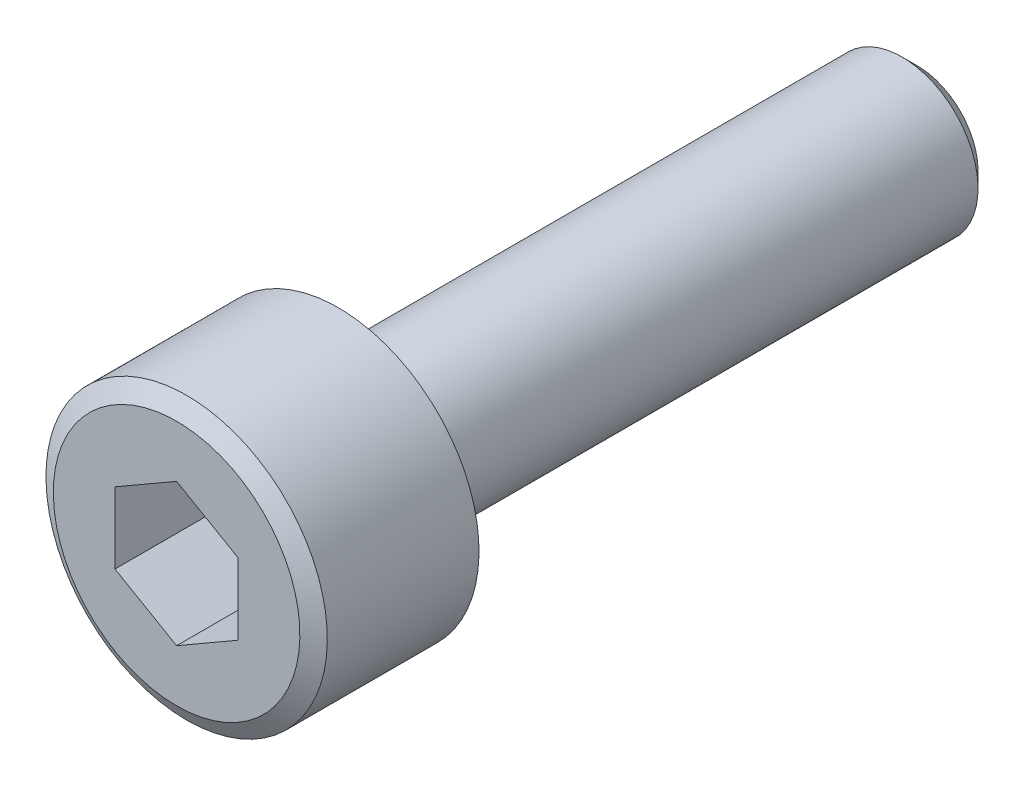
SolidWorks part; units mm, degrees
ref_plane "Front Plane" through (0, 0, 0) normal (0, 0, 1) x (1, 0, 0)
ref_plane "Top Plane" through (0, 0, 0) normal (0, 1, 0) x (1, 0, 0)
ref_plane "Right Plane" through (0, 0, 0) normal (1, 0, 0) x (0, 0, -1)
sketch "Sketch1" plane through (0, 0, 0) normal (1, 0, 0) x (0, 0, -1)
  line L0 (0, 0) -> (39.06, 0) construction
  line L1 (0, 0) -> (0, 6.5)
  line L2 (0, 6.5) -> (0.53, 7.418)
  line L3 (0.53, 7.418) -> (8.53, 7.418)
  line L4 (8.53, 7.418) -> (9.06, 6.5)
  line L5 (9.06, 6.5) -> (9.06, 4)
  line L6 (9.06, 4) -> (39.06, 4)
  line L7 (39.06, 4) -> (39.06, 0)
  line L8 (0, 0) -> (39.06, 0)
  dimension "D1" = 4
  dimension "D2" = 30
  dimension "D3" = 8
  dimension "D4" = 30
  dimension "D5" = 30
  dimension "D6" = 6.5
  dimension "D7" = 0.53
  dimension "D8" = 0.53
revolve "Revolve1" add sketch "Sketch1" angle 360 about L0
chamfer "Chamfer1" distance 0.8 angle 45 1 edges at (0, -4, -39.06)
sketch "Sketch2" plane through (0, 0, 0) normal (0, 0, 1) x (1, 0, 0)
  line L1 (-3.25, 1.8764) -> (-3.25, -1.8764)
  line L2 (-3.25, -1.8764) -> (0, -3.7528)
  line L3 (0, -3.7528) -> (3.25, -1.8764)
  line L4 (3.25, -1.8764) -> (3.25, 1.8764)
  line L5 (3.25, 1.8764) -> (0, 3.7528)
  line L6 (0, 3.7528) -> (-3.25, 1.8764)
  circle A0 centre (0, 0) radius 3.25 construction
  dimension "D1" = 6.5
extrude "Cut-Extrude1" cut sketch "Sketch2" against normal blind 6
sketch "Sketch3" plane through (0, 0, 0) normal (1, 0, 0) x (0, 0, -1)
  line L0 (0, 0) -> (10.0456, 0) construction
  line L1 (0, 0) -> (0, 4)
  line L2 (0, 6.5) -> (0, -6.5) construction
  line L3 (0, 4) -> (2.3094, 0)
  line L4 (6, 0) -> (6, 3.7528)
  line L5 (6, -1.8764) -> (6, 1.8764) construction
  line L6 (6, 3.7528) -> (8.1667, 0)
  line L7 (8.1667, 0) -> (6, 0)
  dimension "D1" = 30
  dimension "D2" = 30
  dimension "D3" = 4
revolve "Cut-Revolve2" cut sketch "Sketch3" angle 360 about L0
sketch "Sketch4" plane through (0, 0, -39.06) normal (0, 0, -1) x (-1, 0, 0)
  circle A1 centre (0, 0) radius 4
  circle A2 centre (0, 0) radius 4
  dimension "D1" = 0
curve "Helix/Spiral1" parameters "D10001"=28, "D30001"=8, "D40001"=1.25, "D10002"=2, "D30002"=16, "D40002"=1.25, "D50000"=1.25
sketch "Sketch5" plane through (0, 0, 0) normal (1, 0, 0) x (0, 0, -1)
  line L0 (37.9608, 5.1389) -> (40.1592, 5.1389)
  line L1 (40.1592, 5.1389) -> (39.06, 3.235)
  line L2 (39.06, 3.235) -> (37.9608, 5.1389)
  line L3 (39.0475, 0) -> (43.2371, 0) construction
  line L13 (39.06, -3.2) -> (39.06, 3.2) construction
  point P6 (0, 0)
  point P7 (0, 0)
  point P8 (0, 0)
  dimension "D1" = 60
